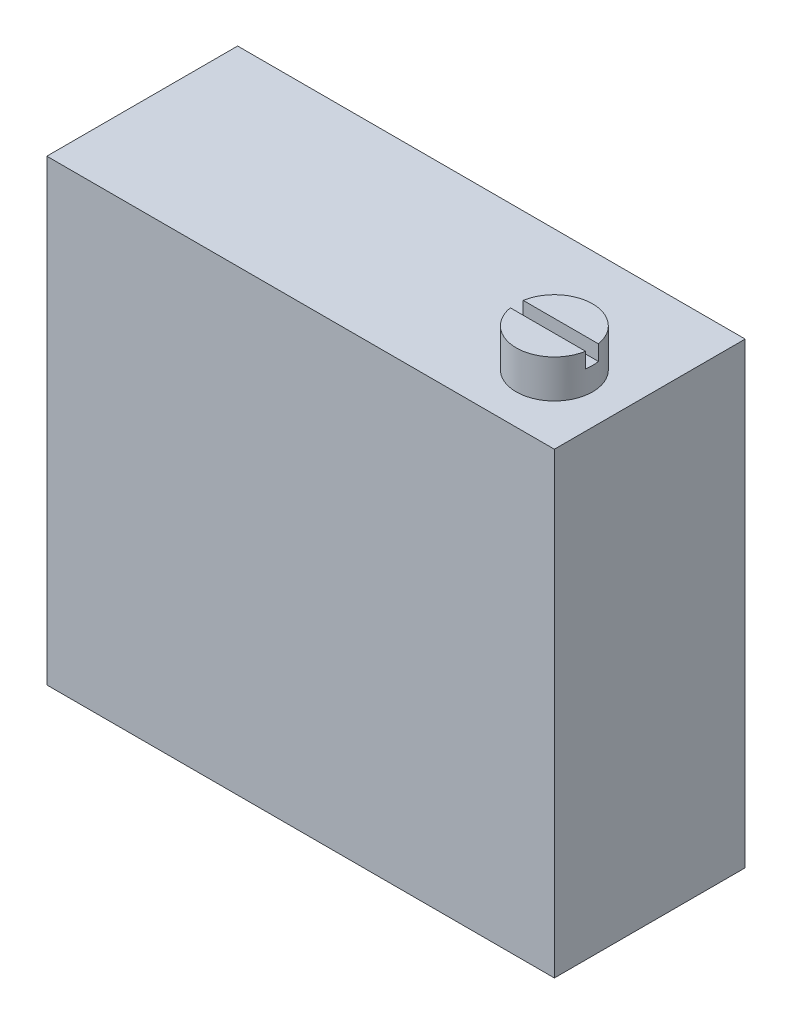
SolidWorks part; units mm, degrees
ref_plane "Спереди" through (0, 0, 0) normal (0, 0, 1) x (1, 0, 0)
ref_plane "Сверху" through (0, 0, 0) normal (0, 1, 0) x (1, 0, 0)
ref_plane "Справа" through (0, 0, 0) normal (1, 0, 0) x (0, 0, -1)
sketch "Эскиз1" plane through (0, 0, 0) normal (0, 1, 0) x (1, 0, 0)
  line L1 (-44.9993, -16.0265) -> (-31.6993, -16.0265)
  line L2 (-44.9993, -16.0265) -> (-44.9993, -21.0265)
  line L3 (-44.9993, -21.0265) -> (-31.6993, -21.0265)
  line L4 (-31.6993, -16.0265) -> (-31.6993, -21.0265)
extrude "Бобышка-Вытянуть1" add sketch "Эскиз1" along normal blind 12
sketch "Эскиз2" plane through (0, 12, 0) normal (0, 1, 0) x (1, 0, 0)
  circle A0 centre (-33.4993, -19.2265) radius 1
extrude "Бобышка-Вытянуть2" add sketch "Эскиз2" along normal blind 1
sketch "Эскиз3" plane through (0, 13, 0) normal (0, 1, 0) x (1, 0, 0)
  line L1 (-34.8686, -19.3952) -> (-32.13, -19.3952)
  line L2 (-34.8686, -19.3952) -> (-34.8686, -19.0577)
  line L3 (-34.8686, -19.0577) -> (-32.13, -19.0577)
  line L4 (-32.13, -19.3952) -> (-32.13, -19.0577)
  line L5 (-34.8686, -19.3952) -> (-32.13, -19.0577) construction
  line L6 (-34.8686, -19.0577) -> (-32.13, -19.3952) construction
  point P0 (-33.4993, -19.2265)
extrude "Вырез-Вытянуть1" cut sketch "Эскиз3" against normal blind 0.4
